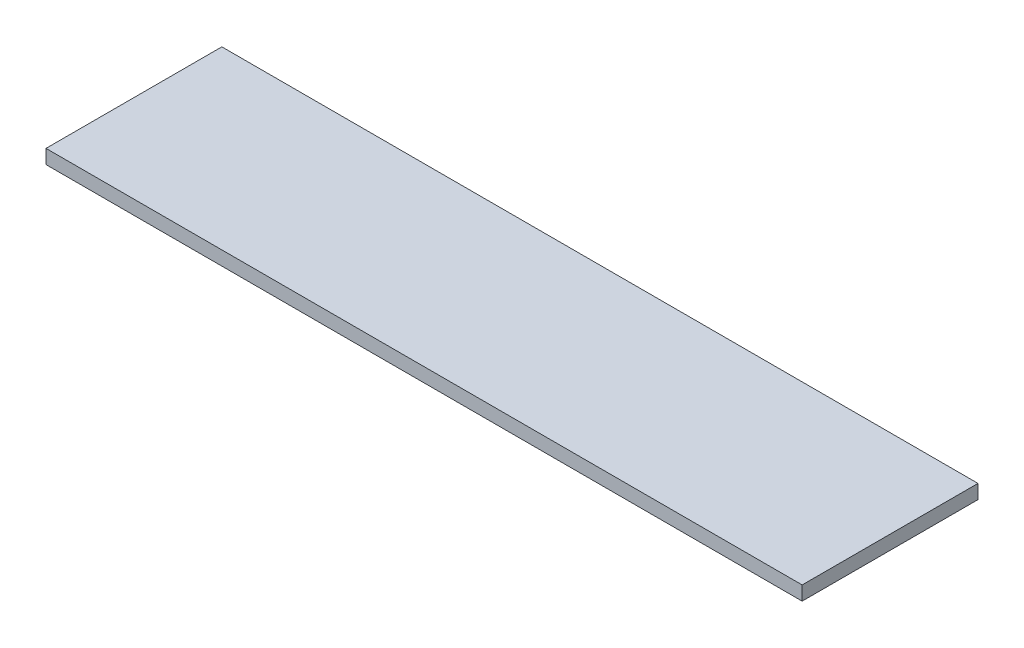
SolidWorks part; units mm, degrees
ref_plane "Front Plane" through (0, 0, 0) normal (0, 0, 1) x (1, 0, 0)
ref_plane "Top Plane" through (0, 0, 0) normal (0, 1, 0) x (1, 0, 0)
ref_plane "Right Plane" through (0, 0, 0) normal (1, 0, 0) x (0, 0, -1)
sketch "Sketch1" plane through (0, 0, 0) normal (0, 1, 0) x (1, 0, 0)
  line L1 (-136.525, -31.75) -> (136.525, -31.75)
  line L2 (-136.525, -31.75) -> (-136.525, 31.75)
  line L3 (-136.525, 31.75) -> (136.525, 31.75)
  line L4 (136.525, -31.75) -> (136.525, 31.75)
  line L5 (-136.525, -31.75) -> (136.525, 31.75) construction
  line L6 (-136.525, 31.75) -> (136.525, -31.75) construction
  point P0 (0, 0)
  dimension "D1" = 63.5
  dimension "D2" = 273.05
extrude "Boss-Extrude1" add sketch "Sketch1" along normal mid plane 5.08
